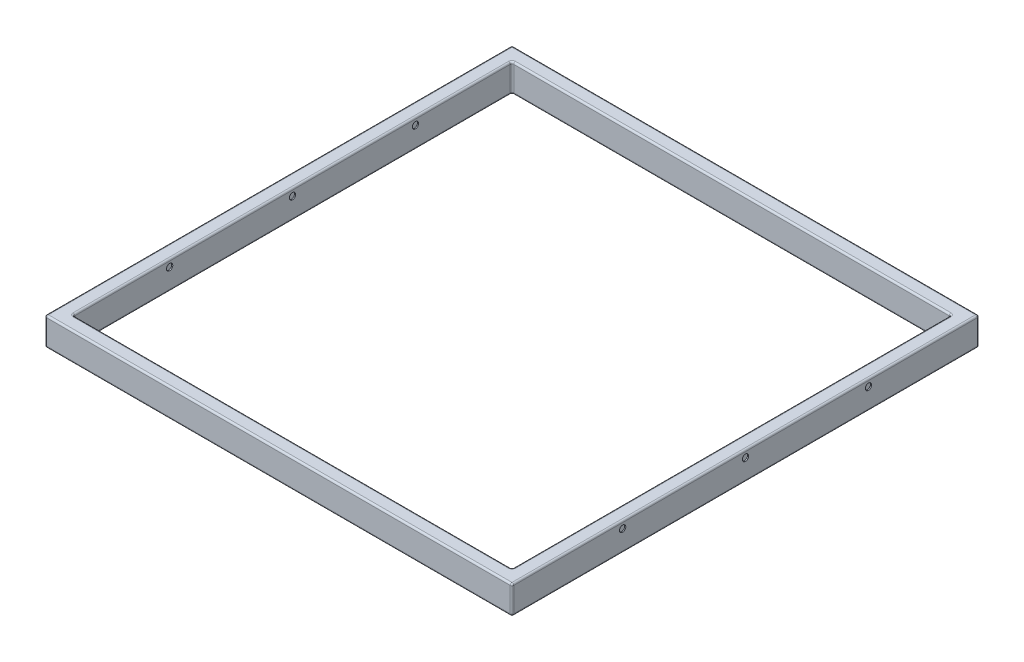
SolidWorks part; units mm, degrees
material "Plain Carbon Steel"
ref_plane "Front" through (0, 0, 0) normal (0, 0, 1) x (1, 0, 0)
ref_plane "Top" through (0, 0, 0) normal (0, 1, 0) x (1, 0, 0)
ref_plane "Right" through (0, 0, 0) normal (1, 0, 0) x (0, 0, -1)
sketch "Sketch1" plane through (0, 0, 0) normal (0, 1, 0) x (1, 0, 0)
  line L1 (-665, 665) -> (665, 665)
  line L2 (-665, 665) -> (-665, -665)
  line L3 (-665, -665) -> (665, -665)
  line L4 (665, 665) -> (665, -665)
  line L5 (-665, 665) -> (665, -665) construction
  line L6 (-665, -665) -> (665, 665) construction
  line L7 (-625, 625) -> (625, 625)
  line L8 (-625, 625) -> (-625, -625)
  line L9 (-625, -625) -> (625, -625)
  line L10 (625, 625) -> (625, -625)
  line L11 (-625, 625) -> (625, -625) construction
  line L12 (-625, -625) -> (625, 625) construction
  point P0 (0, 0)
  point P6 (0, 0)
  dimension "D1" = 1330
  dimension "D2" = 40
extrude "Boss-Extrude1" add sketch "Sketch1" along normal blind 80
fillet "Fillet1" radius 5 24 edges at (-665, 40, 665) (665, 40, 665) (0, 0, 665) (0, 80, 665) (-665, 80, 0) (0, 80, -665) (665, 80, 0) (-625, 80, 0) (0, 80, 625) (625, 80, 0) (0, 80, -625) (665, 40, -665) (-665, 40, -665) (-665, 0, 0) (0, 0, -665) (665, 0, 0) (625, 40, -625) (-625, 40, -625) (-625, 40, 625) (625, 40, 625) (0, 0, 625) (-625, 0, 0) (0, 0, -625) (625, 0, 0)
shell "Shell1" thickness 3
sketch "Sketch2" plane through (665, 0, 0) normal (1, 0, 0) x (0, 0, -1)
  circle A0 centre (-350, 60) radius 9
  circle A1 centre (0, 60) radius 9
  circle A2 centre (350, 60) radius 9
  dimension "D1" = 18
extrude "Cut-Extrude1" cut sketch "Sketch2" against normal up to surface (40 mm away) up to face at (625, 40, 0)
sketch "Sketch3" plane through (-665, 0, 0) normal (-1, 0, 0) x (0, 0, 1)
  circle A1 centre (-350, 60) radius 9
  circle A2 centre (-350, 60) radius 9
  circle A3 centre (0, 60) radius 9
  circle A4 centre (0, 60) radius 9
  circle A5 centre (350, 60) radius 9
  circle A6 centre (350, 60) radius 9
  dimension "D1" = 0
  dimension "D2" = 0
  dimension "D3" = 0
extrude "Cut-Extrude2" cut sketch "Sketch3" against normal up to surface (40 mm away) up to face at (-625, 40, 0)
